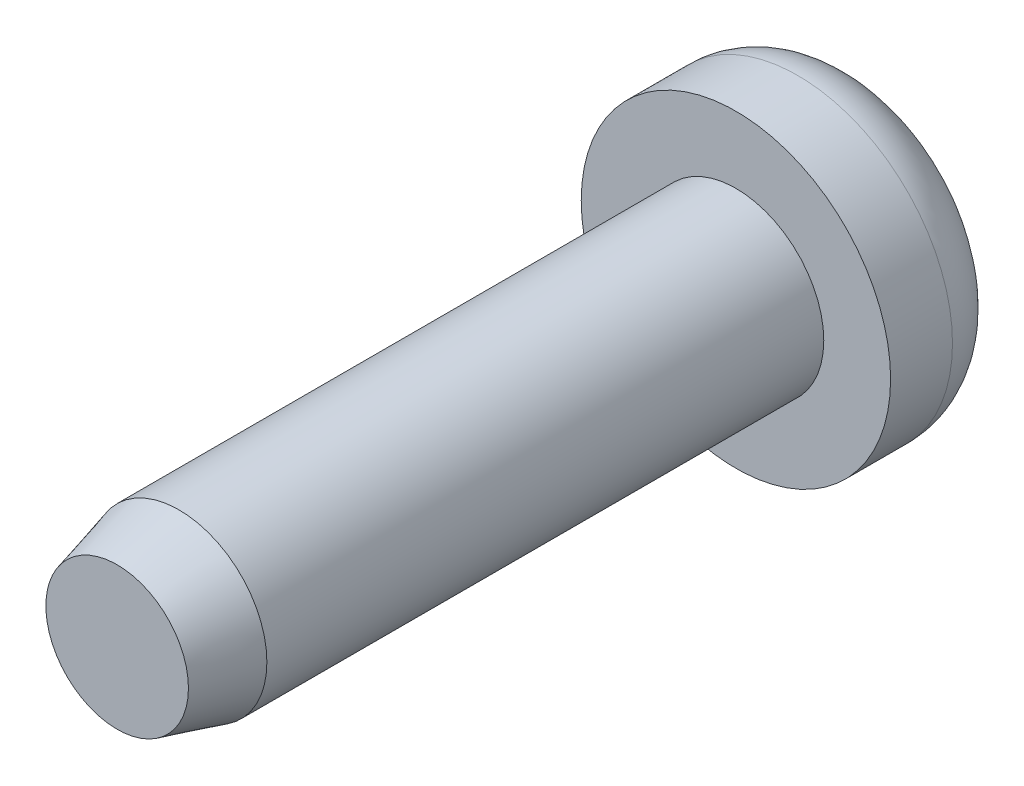
SolidWorks part; units mm, degrees
ref_plane "Front Plane" through (0, 0, 0) normal (0, 0, 1) x (1, 0, 0)
ref_plane "Top Plane" through (0, 0, 0) normal (0, 1, 0) x (1, 0, 0)
ref_plane "Right Plane" through (0, 0, 0) normal (1, 0, 0) x (0, 0, -1)
sketch "Sketch1" plane through (0, 0, 0) normal (0, 0, 1) x (1, 0, 0)
  circle A0 centre (0, 0) radius 1.8034
  dimension "D1" = 3.6068
extrude "Boss-Extrude1" add sketch "Sketch1" along normal mid plane 12.7
chamfer "Chamfer1" distance 1.27 angle 15 1 edges at (1.8034, 0, 6.35)
sketch "Sketch2" plane through (0, 0, 0) normal (0, 1, 0) x (1, 0, 0)
  line L0 (1.8034, 6.35) -> (-1.8034, 6.35) construction
  line L1 (0, 6.35) -> (3.175, 6.35)
  line L2 (0, 6.35) -> (0, 8.89)
  line L3 (0, 8.89) -> (1.905, 8.89)
  line L4 (3.175, 6.35) -> (3.175, 7.62)
  arc A0 (1.905, 8.89) -> (3.175, 7.62) centre (1.905, 7.62) cw
  point P8 (3.175, 8.89)
  dimension "D3" = 1.27
  dimension "D1" = 2.54
  dimension "D2" = 3.175
revolve "Revolve1" add sketch "Sketch2" angle 360 about L2
